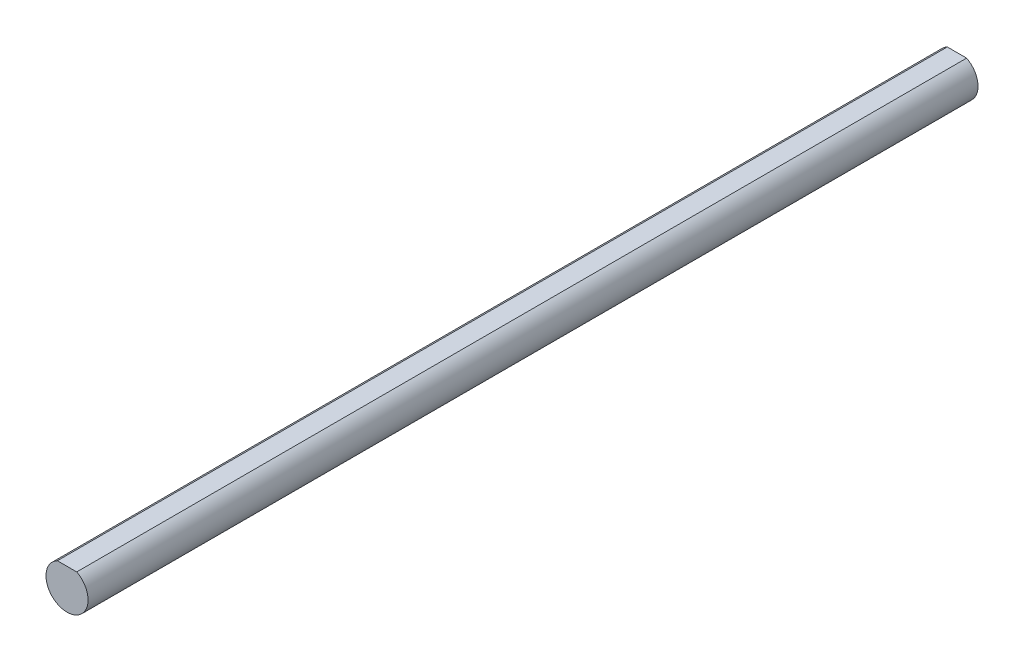
SolidWorks part; units mm, degrees
material "Alloy Steel"
ref_plane "Front Plane" through (0, 0, 0) normal (0, 0, 1) x (1, 0, 0)
ref_plane "Top Plane" through (0, 0, 0) normal (0, 1, 0) x (1, 0, 0)
ref_plane "Right Plane" through (0, 0, 0) normal (1, 0, 0) x (0, 0, -1)
sketch "Sketch1" plane through (0, 0, 0) normal (0, 0, 1) x (1, 0, 0)
  line L0 (-1.0878, 2.1) -> (1.0878, 2.1)
  arc A0 (-1.0878, 2.1) -> (1.0878, 2.1) centre (0, 0) ccw
  dimension "D1" = 4.73
  dimension "D2" = 2.1
extrude "Extrude1" add sketch "Sketch1" against normal mid plane 100
